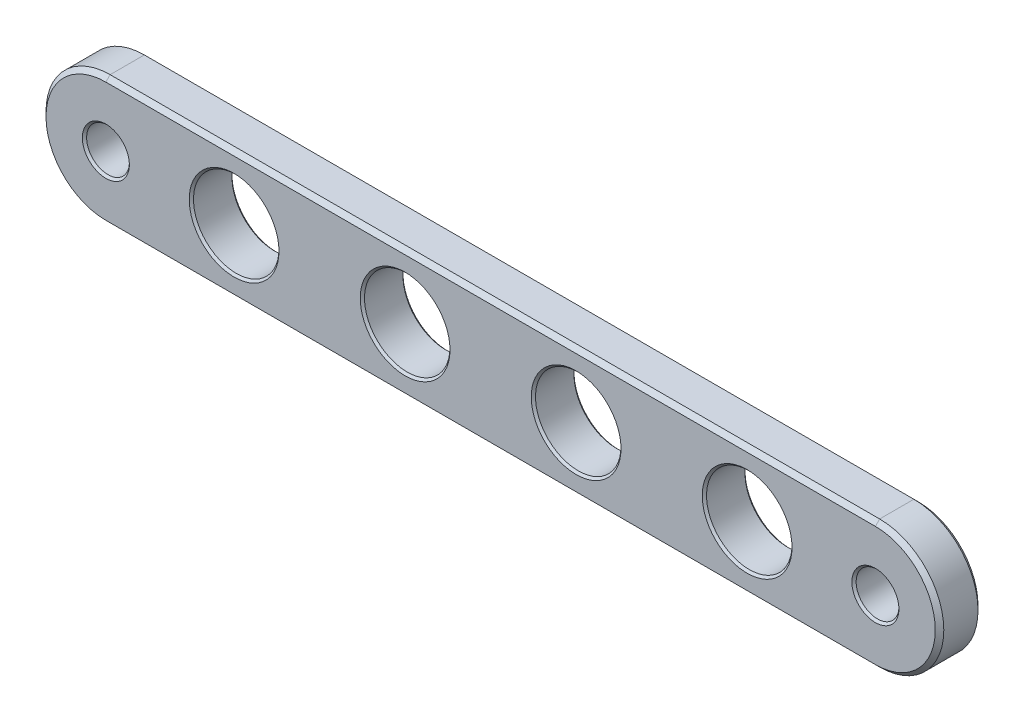
SolidWorks part; units mm, degrees
material "Copper"
ref_plane "Front Plane" through (0, 0, 0) normal (0, 0, 1) x (1, 0, 0)
ref_plane "Top Plane" through (0, 0, 0) normal (0, 1, 0) x (1, 0, 0)
ref_plane "Right Plane" through (0, 0, 0) normal (1, 0, 0) x (0, 0, -1)
sketch "Sketch1" plane through (0, 0, 0) normal (0, 0, 1) x (1, 0, 0)
  line L0 (-18, 0) -> (18, 0) construction
  line L1 (-18, 3) -> (18, 3)
  line L2 (-18, -3) -> (18, -3)
  line L3 (0, 0) -> (0, 8.2155) construction
  arc A0 (-18, 3) -> (-18, -3) centre (-18, 0) ccw
  arc A1 (18, -3) -> (18, 3) centre (18, 0) ccw
  point P2 (0, 0)
  point P4 (0, 0)
  dimension "D2" = 3
  dimension "D1" = 36
extrude "Boss-Extrude1" add sketch "Sketch1" along normal blind 2
chamfer "Chamfer3" distance 0.2 angle 45 8 edges at (0, 3, 0) (-21, 0, 0) (21, 0, 0) (0, -3, 0) (0, 3, 2) (-21, 0, 2) (21, 0, 2) (0, -3, 2)
sketch "Sketch4" plane through (0, 0, 2) normal (0, 0, 1) x (1, 0, 0)
  line L0 (0, 0) -> (0, 7.8302) construction
  line L1 (18, -1.9669) -> (18, 1.9669) construction
  line L2 (12, -2.8) -> (12, 2.8) construction
  line L3 (18, 2.8) -> (-18, 2.8) construction
  line L4 (4, -2.8) -> (4, 2.8) construction
  line L5 (-4, -2.8) -> (-4, 2.8) construction
  line L6 (-12, -2.8) -> (-12, 2.8) construction
  line L7 (-18, -2.4169) -> (-18, 2.4169) construction
  circle A0 centre (-18, 0) radius 1
  circle A1 centre (-12, 0) radius 2
  circle A2 centre (-4, 0) radius 2
  circle A3 centre (4, 0) radius 2
  circle A4 centre (12, 0) radius 2
  circle A5 centre (18, 0) radius 1
  point P18 (18, 0)
  point P23 (12, 0)
  point P26 (4, 0)
  point P29 (-4, 0)
  point P32 (-12, 0)
  point P35 (-18, 0)
  dimension "D1" = 2
  dimension "D3" = 4
  dimension "D2" = 18
  dimension "D4" = 6
  dimension "D5" = 8
extrude "Cut-Extrude3" cut sketch "Sketch4" against normal blind 2
chamfer "Chamfer5" distance 0.1 angle 45 6 edges at (17, 0, 2) (10, 0, 2) (2, 0, 2) (-2, 0, 2) (-10, 0, 2) (-17, 0, 2)
chamfer "Chamfer6" distance 0.1 angle 45 6 edges at (17, 0, 0) (10, 0, 0) (2, 0, 0) (-2, 0, 0) (-10, 0, 0) (-17, 0, 0)
